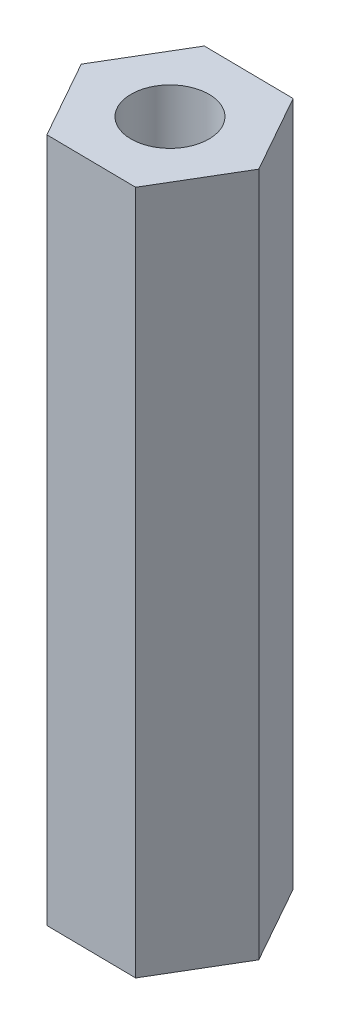
SolidWorks part; units mm, degrees
material "Alloy Steel"
ref_plane "Front Plane" through (0, 0, 0) normal (0, 0, 1) x (1, 0, 0)
ref_plane "Top Plane" through (0, 0, 0) normal (0, 1, 0) x (1, 0, 0)
ref_plane "Right Plane" through (0, 0, 0) normal (1, 0, 0) x (0, 0, -1)
sketch "Sketch1" plane through (0, 0, 0) normal (0, 1, 0) x (1, 0, 0)
  line L1 (1.4132, -2.5172) -> (2.8865, -0.0348)
  line L2 (2.8865, -0.0348) -> (1.4734, 2.4824)
  line L3 (1.4734, 2.4824) -> (-1.4132, 2.5172)
  line L4 (-1.4132, 2.5172) -> (-2.8865, 0.0348)
  line L5 (-2.8865, 0.0348) -> (-1.4734, -2.4824)
  line L6 (-1.4734, -2.4824) -> (1.4132, -2.5172)
  circle A0 centre (0, 0) radius 2.5 construction
  dimension "D1" = 5
extrude "Boss-Extrude1" add sketch "Sketch1" along normal blind 22
sketch "Sketch2" plane through (0, 22, 0) normal (0, 1, 0) x (1, 0, 0)
  point P0 (0, 0)
hole_wizard "M3x0.5 Tapped Hole1" positions "Sketch3" profile "Sketch4" tap size "M3x0.5" standard "ANSI Metric" end condition up to next
sketch "Sketch3" plane through (0, 22, 0) normal (0, 1, 0) x (1, 0, 0)
  point P0 (0, 0)
sketch "Sketch4" plane through (0, 22, 0) normal (1, 0, 0) x (0, 0, 1)
  line L0 (0, 0) -> (0, 22)
  line L1 (0, 22) -> (1.25, 22)
  line L2 (1.25, 22) -> (1.25, 0)
  line L5 (1.25, 0) -> (0, 0)
  line L11 (0, -6.35) -> (0, 107.95) construction
  dimension "Thru Tap Drill Dia." = 2.5
  dimension "Thru Tap Drill Depth" = 22
cosmetic thread "Hole Thread1" parameters "D2"=3
